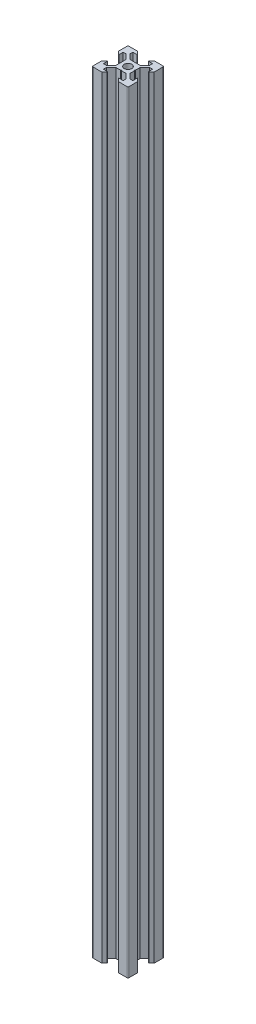
SolidWorks part; units mm, degrees
ref_plane "Front Plane" through (0, 0, 0) normal (0, 0, 1) x (1, 0, 0)
ref_plane "Top Plane" through (0, 0, 0) normal (0, 1, 0) x (1, 0, 0)
ref_plane "Right Plane" through (0, 0, 0) normal (1, 0, 0) x (0, 0, -1)
ref_plane "Plane1" through (0, -10, 0) normal (0, 1, 0) x (1, 0, 0)
sketch "Sketch1" plane through (0, -10, 0) normal (0, 1, 0) x (1, 0, 0)
  line L0 (419, 554.5) -> (419, 549.58)
  line L1 (419, 549.58) -> (420.455, 548.125)
  line L2 (420.455, 548.125) -> (420.8, 548.125)
  line L3 (420.8, 548.125) -> (420.8, 550.5)
  line L4 (420.8, 550.5) -> (422.4393, 550.5)
  line L5 (422.4393, 550.5) -> (425.1, 547.8393)
  line L6 (425.1, 547.8393) -> (425.1, 545.21)
  line L7 (425.1, 545.21) -> (425.31, 545)
  line L8 (425.31, 545) -> (425.1, 544.79)
  line L9 (425.1, 544.79) -> (425.1, 542.1607)
  line L10 (425.1, 542.1607) -> (422.4393, 539.5)
  line L11 (422.4393, 539.5) -> (420.8, 539.5)
  line L12 (420.8, 539.5) -> (420.8, 541.875)
  line L13 (420.8, 541.875) -> (420.455, 541.875)
  line L14 (420.455, 541.875) -> (419, 540.42)
  line L15 (419, 540.42) -> (419, 535.5)
  line L16 (419.5, 535) -> (424.42, 535)
  line L17 (424.42, 535) -> (425.875, 536.455)
  line L18 (425.875, 536.455) -> (425.875, 536.8)
  line L19 (425.875, 536.8) -> (423.5, 536.8)
  line L20 (423.5, 536.8) -> (423.5, 538.4393)
  line L21 (423.5, 538.4393) -> (426.1607, 541.1)
  line L22 (426.1607, 541.1) -> (428.79, 541.1)
  line L23 (428.79, 541.1) -> (429, 541.31)
  line L24 (429, 541.31) -> (429.21, 541.1)
  line L25 (429.21, 541.1) -> (431.8393, 541.1)
  line L26 (431.8393, 541.1) -> (434.5, 538.4393)
  line L27 (434.5, 538.4393) -> (434.5, 536.8)
  line L28 (434.5, 536.8) -> (432.125, 536.8)
  line L29 (432.125, 536.8) -> (432.125, 536.455)
  line L30 (432.125, 536.455) -> (433.58, 535)
  line L31 (433.58, 535) -> (438.5, 535)
  line L32 (439, 535.5) -> (439, 540.42)
  line L33 (439, 540.42) -> (437.545, 541.875)
  line L34 (437.545, 541.875) -> (437.2, 541.875)
  line L35 (437.2, 541.875) -> (437.2, 539.5)
  line L36 (437.2, 539.5) -> (435.5607, 539.5)
  line L37 (435.5607, 539.5) -> (432.9, 542.1607)
  line L38 (432.9, 542.1607) -> (432.9, 544.79)
  line L39 (432.9, 544.79) -> (432.69, 545)
  line L40 (432.69, 545) -> (432.9, 545.21)
  line L41 (432.9, 545.21) -> (432.9, 547.8393)
  line L42 (432.9, 547.8393) -> (435.5607, 550.5)
  line L43 (435.5607, 550.5) -> (437.2, 550.5)
  line L44 (437.2, 550.5) -> (437.2, 548.125)
  line L45 (437.2, 548.125) -> (437.545, 548.125)
  line L46 (437.545, 548.125) -> (439, 549.58)
  line L47 (439, 549.58) -> (439, 554.5)
  line L48 (438.5, 555) -> (433.58, 555)
  line L49 (433.58, 555) -> (432.125, 553.545)
  line L50 (432.125, 553.545) -> (432.125, 553.2)
  line L51 (432.125, 553.2) -> (434.5, 553.2)
  line L52 (434.5, 553.2) -> (434.5, 551.5607)
  line L53 (434.5, 551.5607) -> (431.8393, 548.9)
  line L54 (431.8393, 548.9) -> (429.21, 548.9)
  line L55 (429.21, 548.9) -> (429, 548.69)
  line L56 (429, 548.69) -> (428.79, 548.9)
  line L57 (428.79, 548.9) -> (426.1607, 548.9)
  line L58 (426.1607, 548.9) -> (423.5, 551.5607)
  line L59 (423.5, 551.5607) -> (423.5, 553.2)
  line L60 (423.5, 553.2) -> (425.875, 553.2)
  line L61 (425.875, 553.2) -> (425.875, 553.545)
  line L62 (425.875, 553.545) -> (424.42, 555)
  line L63 (424.42, 555) -> (419.5, 555)
  arc A0 (419, 535.5) -> (419.5, 535) centre (419.5, 535.5) ccw
  arc A1 (438.5, 535) -> (439, 535.5) centre (438.5, 535.5) ccw
  arc A2 (439, 554.5) -> (438.5, 555) centre (438.5, 554.5) ccw
  arc A3 (419.5, 555) -> (419, 554.5) centre (419.5, 554.5) ccw
  circle A4 centre (429, 545) radius 2.1
extrude "Boss-Extrude1" add sketch "Sketch1" against normal blind 430
